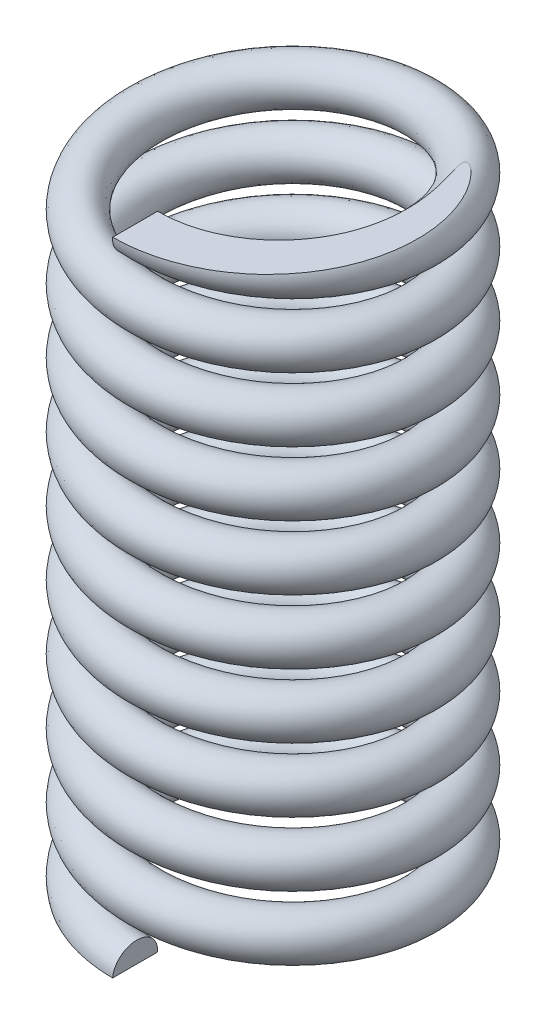
SolidWorks part; units mm, degrees
ref_plane "Front Plane" through (0, 0, 0) normal (0, 0, 1) x (1, 0, 0)
ref_plane "Top Plane" through (0, 0, 0) normal (0, 1, 0) x (1, 0, 0)
ref_plane "Right Plane" through (0, 0, 0) normal (1, 0, 0) x (0, 0, -1)
sketch "Sketch1" plane through (0, 0, 0) normal (0, 1, 0) x (1, 0, 0)
  circle A0 centre (0, 0) radius 2.15
  dimension "D1" = 4.3
curve "Helix/Spiral1" pitch 1 height 10 turns 10
sweep "Sweep2" add path "Helix/Spiral1" circular profile diameter 0.7 parameters "D3"=0.7
sketch "Sketch3" plane through (0, 0, 0) normal (1, 0, 0) x (0, 0, -1)
  line L0 (0, 0) -> (-2.8475, 0)
  line L1 (-2.8475, 0) -> (-2.8475, 10)
  line L2 (-2.8475, 10) -> (0, 10)
  line L3 (0, 10) -> (0, 10.7031)
  line L4 (0, 10.7031) -> (-4.3219, 10.7031)
  line L5 (-4.3219, 10.7031) -> (-4.3219, -0.6056)
  line L6 (-4.3219, -0.6056) -> (0, -0.6056)
  line L7 (0, -0.6056) -> (0, 0)
  dimension "D1" = 10
revolve "Cut-Revolve1" cut sketch "Sketch3" angle 360 about L7
